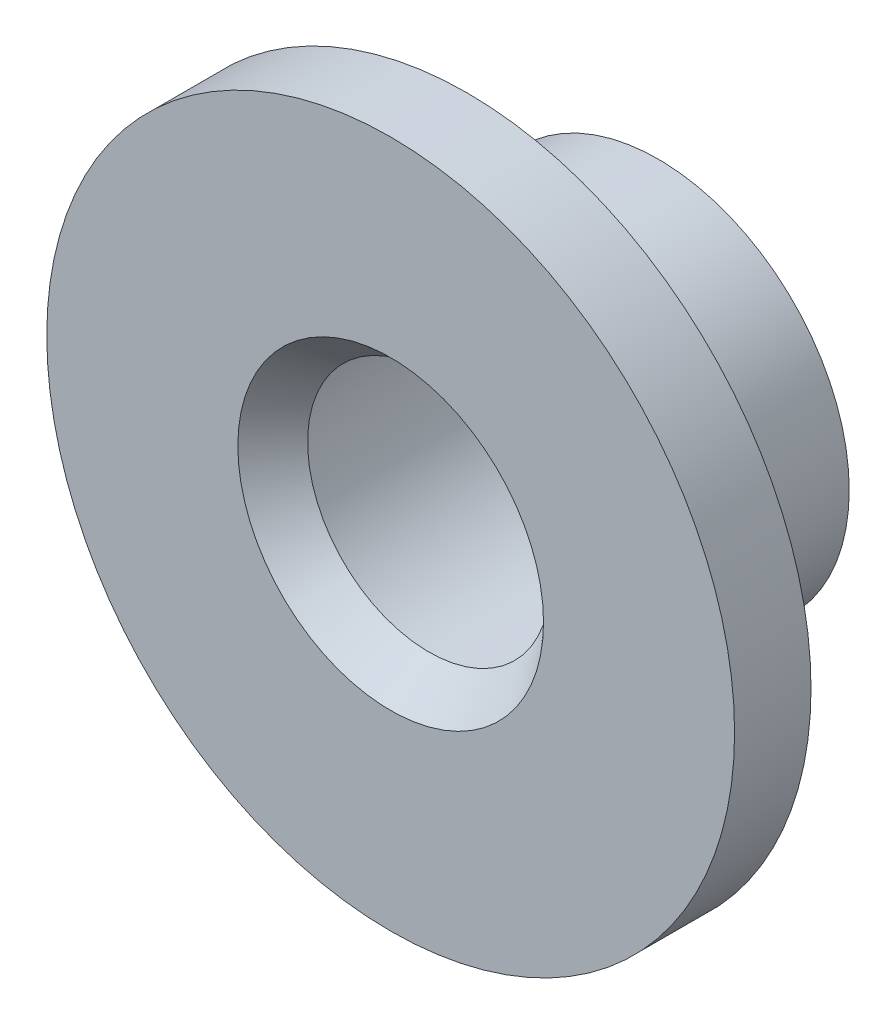
SolidWorks part; units mm, degrees
ref_plane "Front Plane" through (0, 0, 0) normal (0, 0, 1) x (1, 0, 0)
ref_plane "Top Plane" through (0, 0, 0) normal (0, 1, 0) x (1, 0, 0)
ref_plane "Right Plane" through (0, 0, 0) normal (1, 0, 0) x (0, 0, -1)
sketch "Sketch1" plane through (0, 0, 0) normal (1, 0, 0) x (0, 0, -1)
  line L0 (0, 18) -> (0, 8)
  line L3 (0, 8) -> (2, 6.35)
  line L4 (2, 6.35) -> (2, 8)
  line L5 (2, 8) -> (14, 8)
  line L6 (14, 8) -> (14, 10)
  line L7 (14, 10) -> (4, 10)
  line L8 (4, 10) -> (4, 18)
  line L9 (4, 18) -> (0, 18)
  line L10 (0, 0) -> (12.3335, 0) construction
  line L11 (0, 0) -> (0, 3.5658) construction
  dimension "D1" = 4
  dimension "D2" = 20
  dimension "D3" = 12.7
  dimension "D4" = 2
  dimension "D5" = 10
  dimension "D6" = 2
  dimension "D7" = 36
revolve "Revolve1" add sketch "Sketch1" angle 360 about L10
